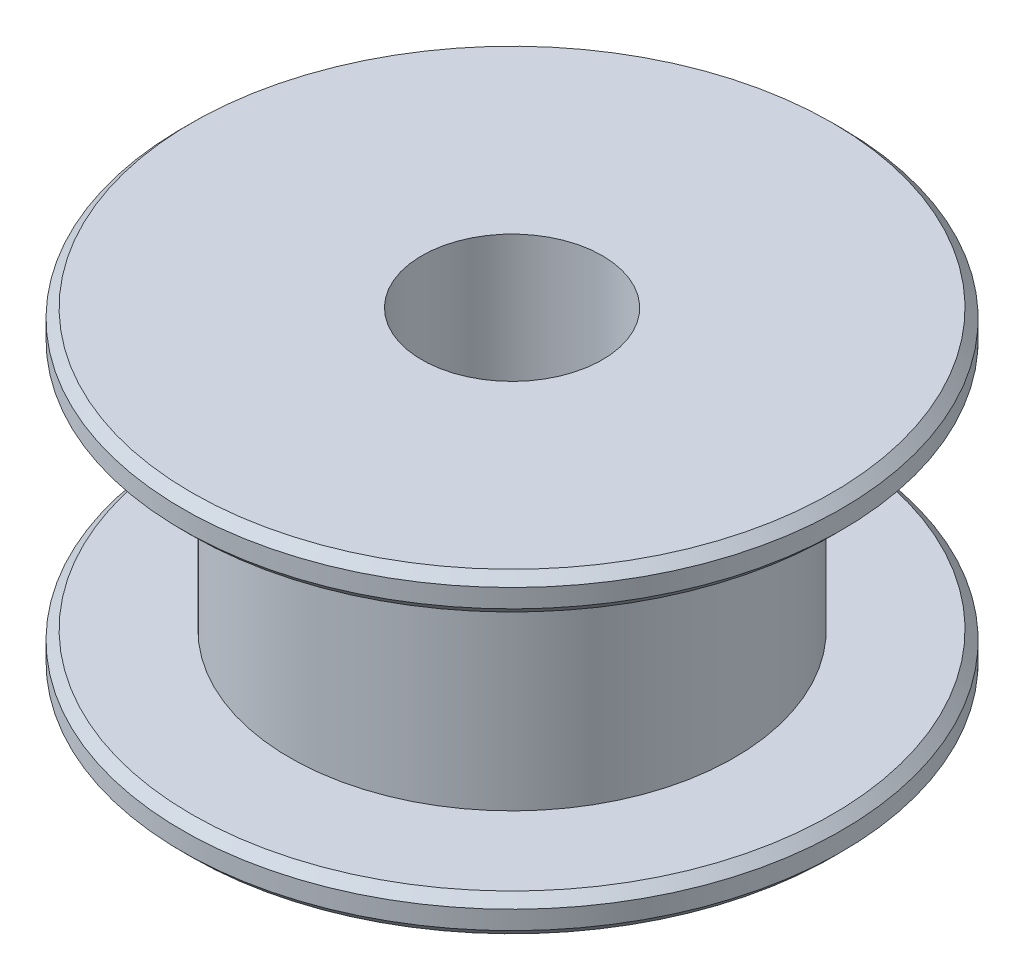
SolidWorks part; units mm, degrees
ref_plane "Front Plane" through (0, 0, 0) normal (0, 0, 1) x (1, 0, 0)
ref_plane "Top Plane" through (0, 0, 0) normal (0, 1, 0) x (1, 0, 0)
ref_plane "Right Plane" through (0, 0, 0) normal (1, 0, 0) x (0, 0, -1)
sketch "Sketch1" plane through (0, 0, 0) normal (0, 0, 1) x (1, 0, 0)
  line L0 (2.4765, 8.6614) -> (2.4765, 0)
  line L1 (2.4765, 0) -> (8.7884, 0)
  line L2 (8.7884, 0) -> (9.0424, 0.254)
  line L3 (9.0424, 0.254) -> (9.0424, 0.762)
  line L4 (9.0424, 0.762) -> (8.7884, 1.016)
  line L5 (8.7884, 1.016) -> (6.096, 1.016)
  line L6 (6.096, 1.016) -> (6.096, 7.6454)
  line L7 (6.096, 7.6454) -> (8.7884, 7.6454)
  line L8 (8.7884, 7.6454) -> (9.0424, 7.8994)
  line L9 (9.0424, 7.8994) -> (9.0424, 8.4074)
  line L10 (9.0424, 8.4074) -> (8.7884, 8.6614)
  line L11 (8.7884, 8.6614) -> (2.4765, 8.6614)
  line L12 (0, 8.6614) -> (0, 0) construction
revolve "Revolve1" add sketch "Sketch1" angle 360 about L12
